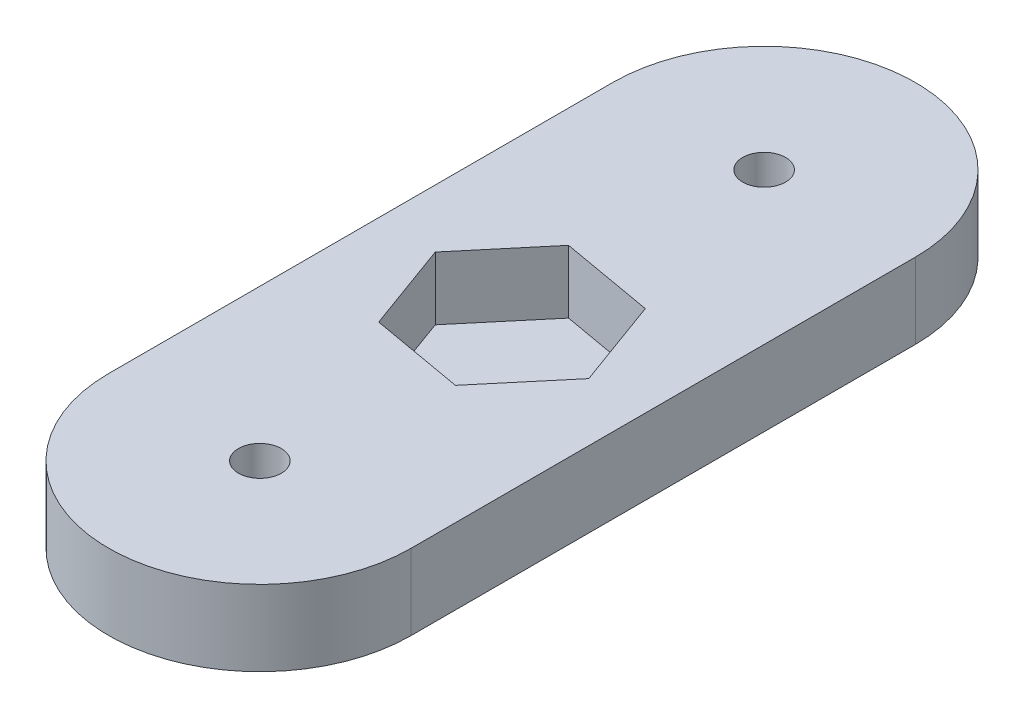
SolidWorks part; units mm, degrees
material "ABS PC"
ref_plane "Front Plane" through (0, 0, 0) normal (0, 0, 1) x (1, 0, 0)
ref_plane "Top Plane" through (0, 0, 0) normal (0, 1, 0) x (1, 0, 0)
ref_plane "Right Plane" through (0, 0, 0) normal (1, 0, 0) x (0, 0, -1)
sketch "Sketch1" plane through (0, 0, 0) normal (0, 1, 0) x (1, 0, 0)
  line L0 (0, 0) -> (0, 40) construction
  line L1 (-12, 0) -> (-12, 40)
  line L2 (12, 0) -> (12, 40)
  arc A0 (-12, 0) -> (12, 0) centre (0, 0) ccw
  arc A1 (12, 40) -> (-12, 40) centre (0, 40) ccw
  circle A2 centre (0, 40) radius 1.7
  circle A3 centre (0, 0) radius 1.7
  point P3 (0, 20)
  dimension "D2" = 40
  dimension "D3" = 3.4
  dimension "D1" = 24
extrude "Boss-Extrude1" add sketch "Sketch1" along normal blind 6
sketch "Sketch2" plane through (0, 6, 0) normal (0, 1, 0) x (1, 0, 0)
  line L0 (12, 0) -> (12, 40) construction
  line L1 (2.5671, 12.9471) -> (7.3915, 18.6967)
  line L2 (7.3915, 18.6967) -> (4.8245, 25.7496)
  line L3 (4.8245, 25.7496) -> (-2.5671, 27.0529)
  line L4 (-2.5671, 27.0529) -> (-7.3915, 21.3033)
  line L5 (-7.3915, 21.3033) -> (-4.8245, 14.2504)
  line L6 (-4.8245, 14.2504) -> (2.5671, 12.9471)
  line L7 (-12, 40) -> (-12, 0) construction
  circle A0 centre (0, 20) radius 6.5 construction
  dimension "D1" = 13
  dimension "D2" = 12
  dimension "D3" = 20
  dimension "D4" = 80
extrude "Cut-Extrude1" cut sketch "Sketch2" against normal blind 5
